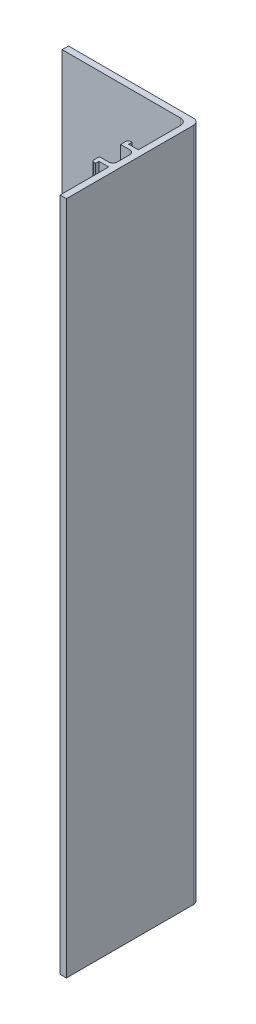
SolidWorks part; units mm, degrees
ref_plane "Alzado" through (0, 0, 0) normal (0, 0, 1) x (1, 0, 0)
ref_plane "Planta" through (0, 0, 0) normal (0, 1, 0) x (1, 0, 0)
ref_plane "Vista lateral" through (0, 0, 0) normal (1, 0, 0) x (0, 0, -1)
sketch "Croquis1" plane through (0, 0, 0) normal (0, 1, 0) x (1, 0, 0)
  line L0 (0, 0) -> (0, 31.5)
  line L1 (0, 31.5) -> (-31, 31.5)
  line L2 (-31, 31.5) -> (-31, 30)
  line L4 (-1.5, 30) -> (-1.5, 18.5)
  line L5 (-1.5, 0) -> (0, 0)
  line L6 (-1.5, 18.5) -> (-3.8, 18.5)
  line L7 (-4.7, 19.3) -> (-4.7, 17.5)
  line L8 (-4.7, 17.5) -> (-1.5, 17.5)
  line L9 (-1.5, 12.5) -> (-4.7, 12.5)
  line L11 (-3.8, 11.5) -> (-1.5, 11.5)
  line L12 (-1.5, 11.5) -> (-1.5, 0)
  line L15 (-4.7, 19.3) -> (-3.8, 19.3)
  line L16 (-3.8, 18.5) -> (-3.8, 19.3)
  line L18 (-4.7, 12.5) -> (-4.7, 10.7)
  line L19 (-4.7, 10.7) -> (-3.8, 10.7)
  line L20 (-3.8, 11.5) -> (-3.8, 10.7)
  line L21 (-1.5, 17.5) -> (-1.5, 12.5)
  line L33 (-31, 30) -> (-1.5, 30)
  point P5 (0, 33.7922)
  point P8 (0, 33.4586)
  point P14 (-37.5684, 29.8445)
  point P22 (-31.3412, 29.9357)
  point P23 (-31, 31.058)
  point P24 (-1.5, 18.3554)
  dimension "D1" = 1.5
  dimension "D2" = 1.5
  dimension "D3" = 29.5
  dimension "D4" = 30
  dimension "D5" = 11.5
  dimension "D6" = 11.5
  dimension "D7" = 3.2
  dimension "D8" = 3.2
  dimension "D9" = 1
  dimension "D10" = 1
  dimension "D11" = 2.3
  dimension "D12" = 0.8
  dimension "D13" = 2.3
  dimension "D14" = 0.8
extrude "Saliente-Extruir1" add sketch "Croquis1" along normal blind 159.5
fillet "Redondeo1" radius 0.5 2 edges at (-4.7, 79.75, -10.7) (-4.7, 79.75, -19.3)
fillet "Redondeo2" radius 1 2 edges at (-1.5, 79.75, -12.5) (-1.5, 79.75, -17.5)
fillet "Redondeo3" radius 1.5 1 edges at (-1.5, 79.75, -30)
fillet "Redondeo4" radius 1.5 1 edges at (0, 79.75, -31.5)
